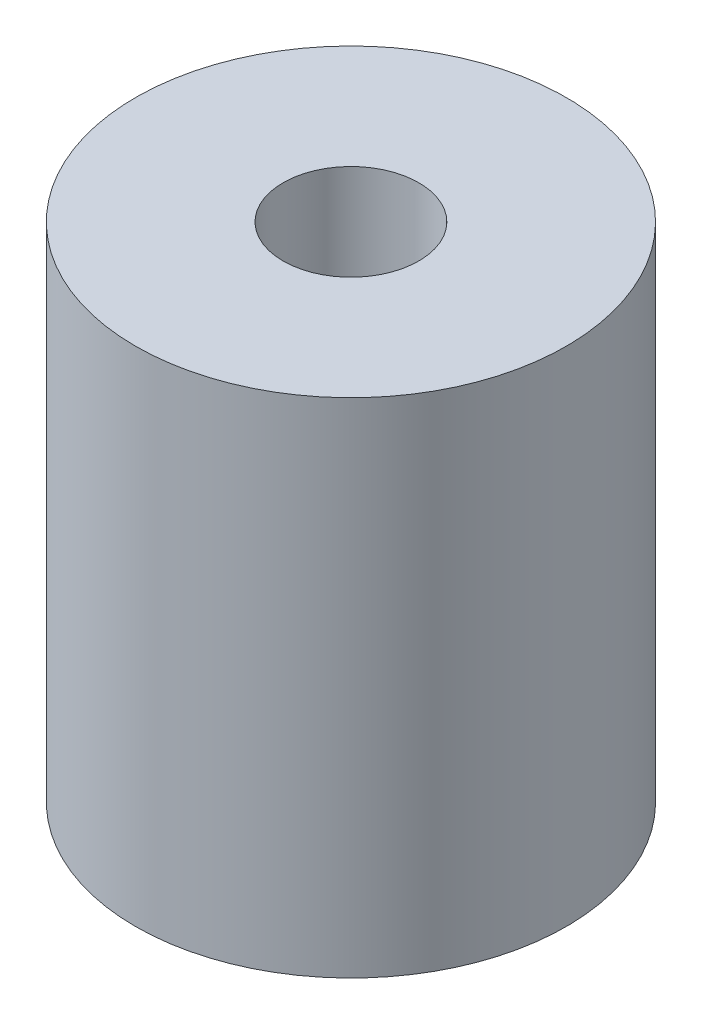
SolidWorks part; units mm, degrees
ref_plane "Front Plane" through (0, 0, 0) normal (0, 0, 1) x (1, 0, 0)
ref_plane "Top Plane" through (0, 0, 0) normal (0, 1, 0) x (1, 0, 0)
ref_plane "Right Plane" through (0, 0, 0) normal (1, 0, 0) x (0, 0, -1)
sketch "Sketch1" plane through (0, 0, 0) normal (0, 1, 0) x (1, 0, 0)
  circle A0 centre (0, 0) radius 4.7625
  circle A1 centre (0, 0) radius 1.5
  dimension "D1" = 3
  dimension "D2" = 9.525
extrude "Extrude1" add sketch "Sketch1" against normal blind 11.1125
